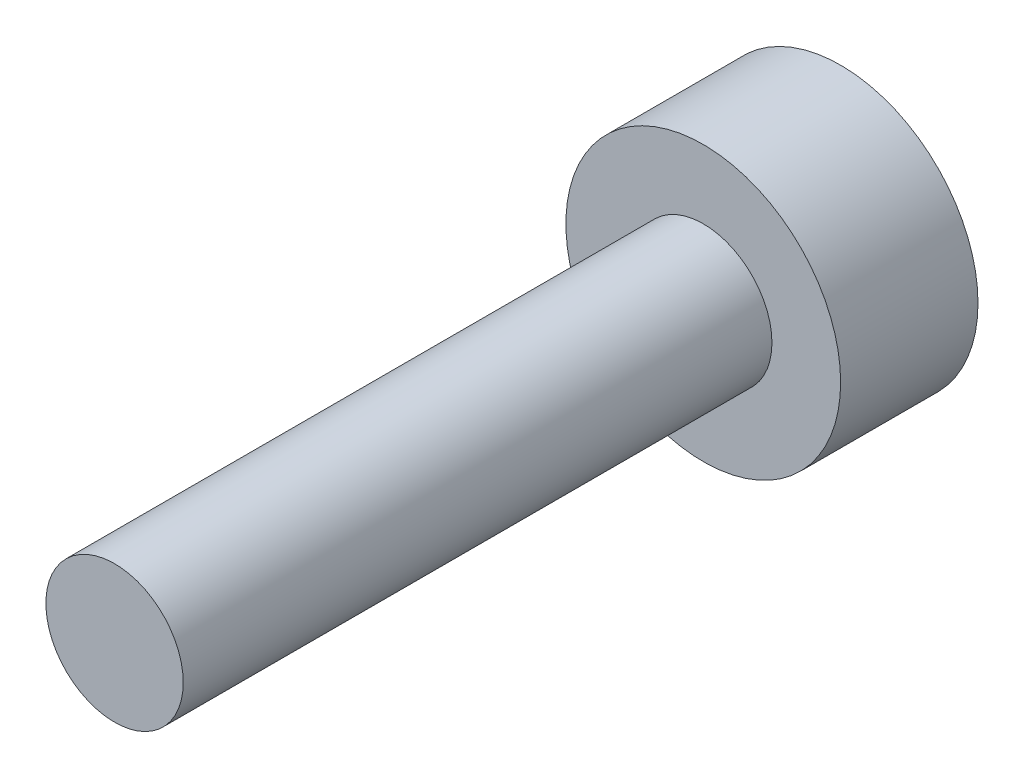
SolidWorks part; units mm, degrees
ref_plane "前视基准面" through (0, 0, 0) normal (0, 0, 1) x (1, 0, 0)
ref_plane "上视基准面" through (0, 0, 0) normal (0, 1, 0) x (1, 0, 0)
ref_plane "右视基准面" through (0, 0, 0) normal (1, 0, 0) x (0, 0, -1)
sketch "草图1" plane through (0, 0, 0) normal (0, 0, 1) x (1, 0, 0)
  circle A0 centre (0, 0) radius 1.4
extrude "凸台-拉伸1" add sketch "草图1" along normal blind 1.4
sketch "草图2" plane through (0, 0, 1.4) normal (0, 0, 1) x (1, 0, 0)
  circle A0 centre (0, 0) radius 0.7
extrude "凸台-拉伸2" add sketch "草图2" along normal blind 10
sketch "草图3" plane through (0, 0, 0) normal (0, 0, -1) x (-1, 0, 0)
  line L1 (0, 0.68) -> (-0.5889, 0.34)
  line L2 (-0.5889, 0.34) -> (-0.5889, -0.34)
  line L3 (-0.5889, -0.34) -> (0, -0.68)
  line L4 (0, -0.68) -> (0.5889, -0.34)
  line L5 (0.5889, -0.34) -> (0.5889, 0.34)
  line L6 (0.5889, 0.34) -> (0, 0.68)
  circle A1 centre (0, 0) radius 0.5889 construction
extrude "切除-拉伸1" cut sketch "草图3" against normal blind 1
sketch "草图4" plane through (0, 0, 11.4) normal (0, 0, 1) x (1, 0, 0)
  circle A0 centre (0, 0) radius 2.875
extrude "切除-拉伸2" cut sketch "草图4" against normal blind 4
